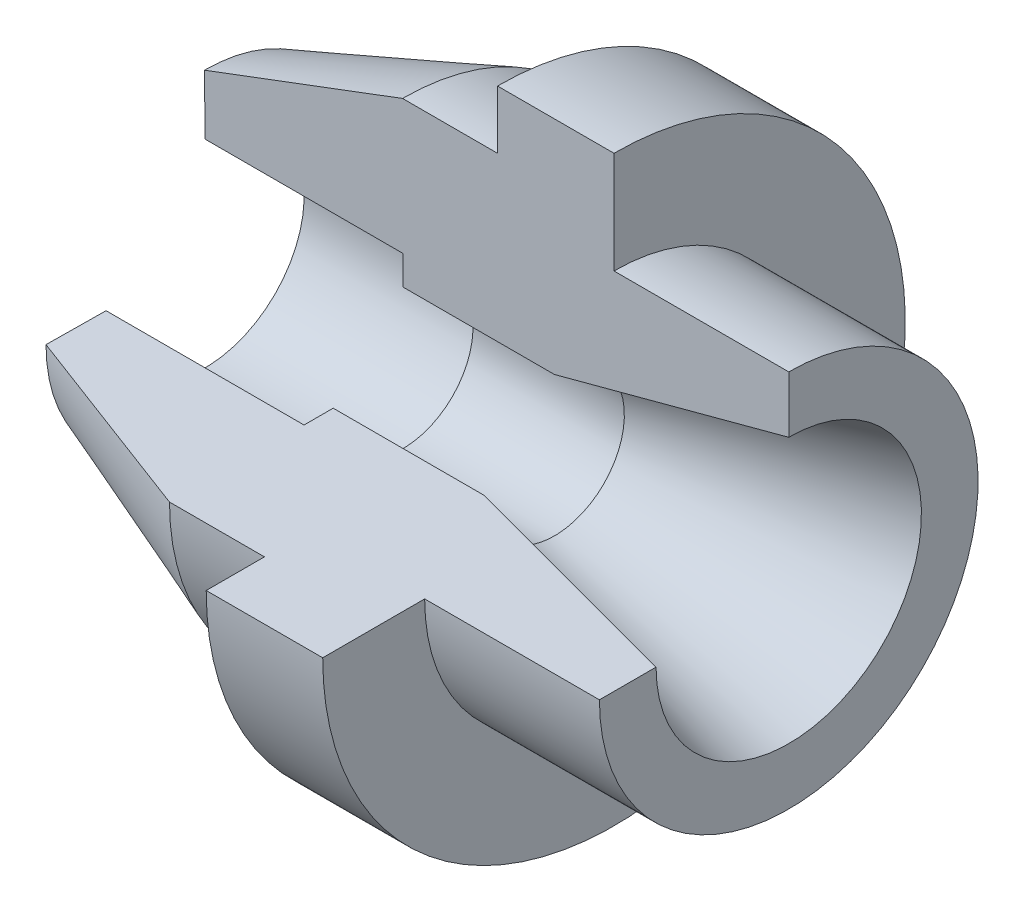
SolidWorks part; units mm, degrees
ref_plane "Front Plane" through (0, 0, 0) normal (0, 0, 1) x (1, 0, 0)
ref_plane "Top Plane" through (0, 0, 0) normal (0, 1, 0) x (1, 0, 0)
ref_plane "Right Plane" through (0, 0, 0) normal (1, 0, 0) x (0, 0, -1)
sketch "Sketch1" plane through (0, 0, 0) normal (0, 0, 1) x (1, 0, 0)
  line L0 (-50, -25) -> (-50.3002, 2.1983)
  line L1 (-50.3002, 2.1983) -> (-16.3002, 15)
  line L2 (-16.3002, 15) -> (0, 15)
  line L3 (0, 15) -> (0, 25)
  line L4 (0, 25) -> (20, 25)
  line L6 (20, 25) -> (20, 7.5)
  line L7 (20, 7.5) -> (50, 7.5)
  line L8 (50, 7.5) -> (50, -25)
  line L9 (50, -25) -> (-50, -25)
  point P5 (0, 0)
  point P7 (0, 0)
  point P11 (-31.3397, 38.6857)
  point P12 (0, 0)
  point P13 (-52.8756, 22.6141)
  point P15 (0, 15)
  point P16 (-16.3002, 15)
  point P17 (0, 25)
  point P18 (0, 0)
  dimension "D1" = 70
  dimension "D2" = 40
  dimension "D3" = 34
  dimension "D4" = 20
  dimension "D5" = 32.5
  dimension "D6" = 50
  dimension "D7" = 30
  dimension "D8" = 100
  dimension "D9" = 27.2
  dimension "D10" = 50
  dimension "D11" = 25
revolve "Revolve1" add sketch "Sketch1" angle 270 about L9
sketch "Sketch2" plane through (0, 0, 0) normal (0, 0, 1) x (1, 0, 0)
  line L0 (-50.1876, -8) -> (-16.2034, -8)
  line L1 (-50.3002, 2.1983) -> (-50, -25) construction
  line L2 (-16.2034, -8) -> (-16.2034, -13)
  line L3 (-16.2034, -13) -> (9.7806, -13)
  line L4 (9.7806, -13) -> (50, -2.2232)
  line L5 (50, -25) -> (50, 7.5) construction
  line L6 (50, -2.2232) -> (50, -25)
  line L7 (50, -25) -> (-50.3002, -25)
  line L8 (-50.3002, -25) -> (-50.1876, -8)
  point P4 (-16.2034, -10.5)
  dimension "D1" = 12
  dimension "D2" = 17
  dimension "D3" = 15
  dimension "D4" = 60
  dimension "D5" = 34
revolve "Cut-Revolve1" cut sketch "Sketch2" angle 360 about L7
